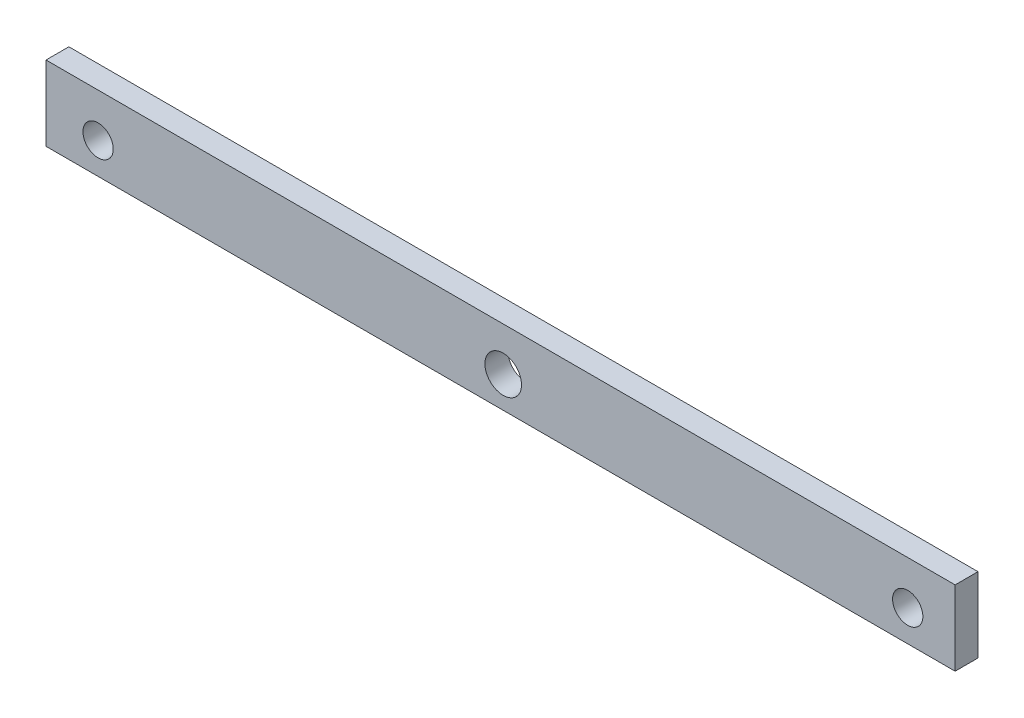
SolidWorks part; units mm, degrees
ref_plane "Front Plane" through (0, 0, 0) normal (0, 0, 1) x (1, 0, 0)
ref_plane "Top Plane" through (0, 0, 0) normal (0, 1, 0) x (1, 0, 0)
ref_plane "Right Plane" through (0, 0, 0) normal (1, 0, 0) x (0, 0, -1)
sketch "Sketch1" plane through (0, 0, 0) normal (0, 0, 1) x (1, 0, 0)
  line L0 (95.6616, -290.9055) -> (95.6616, -242.2903) construction
  line L1 (-63.319, -289.9055) -> (95.6616, -289.9055)
  line L2 (-63.319, -289.9055) -> (-63.319, -302.9837)
  line L3 (-63.319, -302.9837) -> (95.6616, -302.9837)
  line L4 (95.6616, -289.9055) -> (95.6616, -302.9837)
  line L5 (-63.319, -282.0915) -> (-63.319, -233.2848) construction
  line L6 (16.6347, -294.8415) -> (16.6347, -267.4519) construction
  line L7 (96.6616, -289.9055) -> (122.5054, -289.9055) construction
  line L8 (95.6616, -302.9837) -> (97.7616, -302.9837) construction
  arc A4 (-28.4363, -288.9208) -> (-24.0141, -288.9208) centre (-26.2252, -282.9055) ccw construction
  dimension "D4" = 6.4088
  dimension "D3" = 7
extrude "Boss-Extrude1" add sketch "Sketch1" along normal blind 4
hole_wizard "M5 Clearance Hole1" positions "Sketch3" profile "Sketch2" hole size "M5" standard "ISO" end condition through all
sketch "Sketch3" plane through (0, 0, 4) normal (0, 0, 1) x (1, 0, 0)
  point P0 (87.371, -297.5235)
  point P2 (-54.209, -297.5235)
sketch "Sketch2" plane through (87.371, -297.5235, 4) normal (1, 0, 0) x (0, -1, 0)
  line L0 (0, 0) -> (0, 4)
  line L1 (0, 4) -> (2.65, 4)
  line L2 (2.65, 4) -> (2.65, 0)
  line L5 (2.65, 0) -> (0, 0)
  line L11 (0, -6.35) -> (0, 107.95) construction
  dimension "Thru Hole Dia." = 5.3
  dimension "Thru Hole Depth" = 4
hole_wizard "M6 Clearance Hole2" positions "Sketch5" profile "Sketch4" hole size "M6" standard "ISO" end condition through all
sketch "Sketch5" plane through (0, 0, 4) normal (0, 0, 1) x (1, 0, 0)
  point P0 (16.6347, -297.5235)
sketch "Sketch4" plane through (16.6347, -297.5235, 4) normal (1, 0, 0) x (0, -1, 0)
  line L0 (0, 0) -> (0, 4)
  line L1 (0, 4) -> (3.2, 4)
  line L2 (3.2, 4) -> (3.2, 0)
  line L5 (3.2, 0) -> (0, 0)
  line L11 (0, -6.35) -> (0, 107.95) construction
  dimension "Thru Hole Dia." = 6.4
  dimension "Thru Hole Depth" = 4
